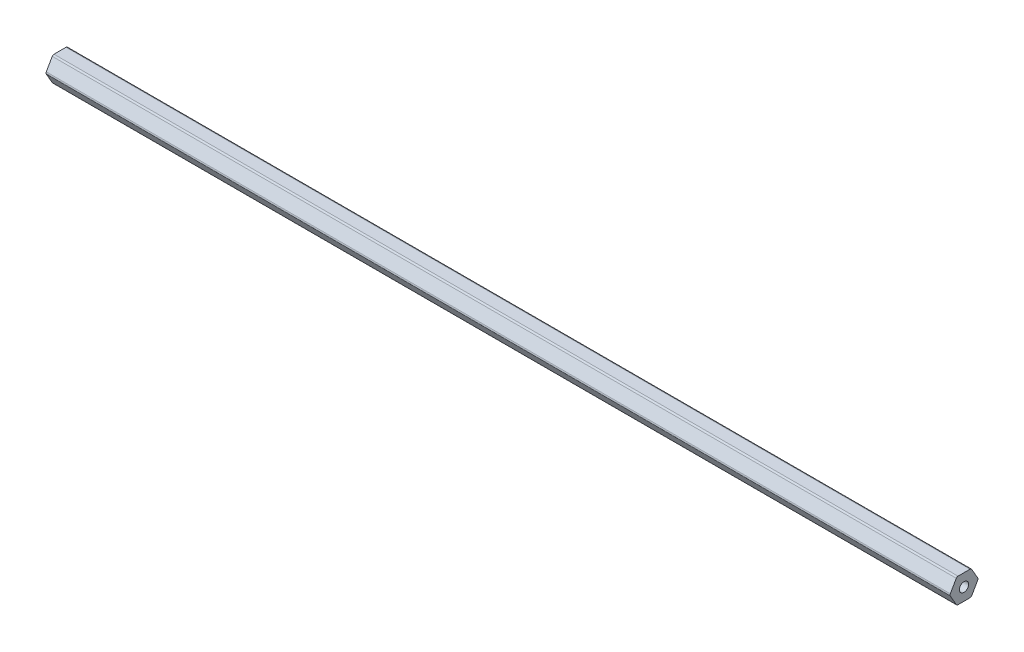
SolidWorks part; units mm, degrees
material "7075-T6 (SN)"
ref_plane "Front Plane" through (0, 0, 0) normal (0, 0, 1) x (1, 0, 0)
ref_plane "Top Plane" through (0, 0, 0) normal (0, 1, 0) x (1, 0, 0)
ref_plane "Right Plane" through (0, 0, 0) normal (1, 0, 0) x (0, 0, -1)
sketch "Sketch1" plane through (0, 0, 0) normal (1, 0, 0) x (0, 0, -1)
  line L1 (7.0391, 0.508) -> (3.9595, 5.842)
  line L2 (3.0796, 6.35) -> (-3.0796, 6.35)
  line L3 (-3.9595, 5.842) -> (-7.0391, 0.508)
  line L4 (-7.0391, -0.508) -> (-3.9595, -5.842)
  line L5 (-3.0796, -6.35) -> (3.0796, -6.35)
  line L6 (3.9595, -5.842) -> (7.0391, -0.508)
  circle A0 centre (0, 0) radius 6.35 construction
  arc A1 (3.0796, 6.35) -> (3.9595, 5.842) centre (3.0796, 5.334) cw
  arc A2 (7.0391, 0.508) -> (7.0391, -0.508) centre (6.1592, 0) cw
  arc A3 (3.9595, -5.842) -> (3.0796, -6.35) centre (3.0796, -5.334) cw
  arc A4 (-3.0796, -6.35) -> (-3.9595, -5.842) centre (-3.0796, -5.334) cw
  arc A5 (-7.0391, -0.508) -> (-7.0391, 0.508) centre (-6.1592, 0) cw
  arc A6 (-3.9595, 5.842) -> (-3.0796, 6.35) centre (-3.0796, 5.334) cw
  circle A7 centre (0, 0) radius 2.3813
  point P11 (3.6662, 6.35)
  point P14 (7.3323, 0)
  dimension "D1" = 12.7
  dimension "D3" = 1.016
  dimension "D4" = 4.7625
  dimension "D2" = 6.35
extrude "Boss-Extrude1" add sketch "Sketch1" along normal blind 231.775 and the other way blind 231.775
